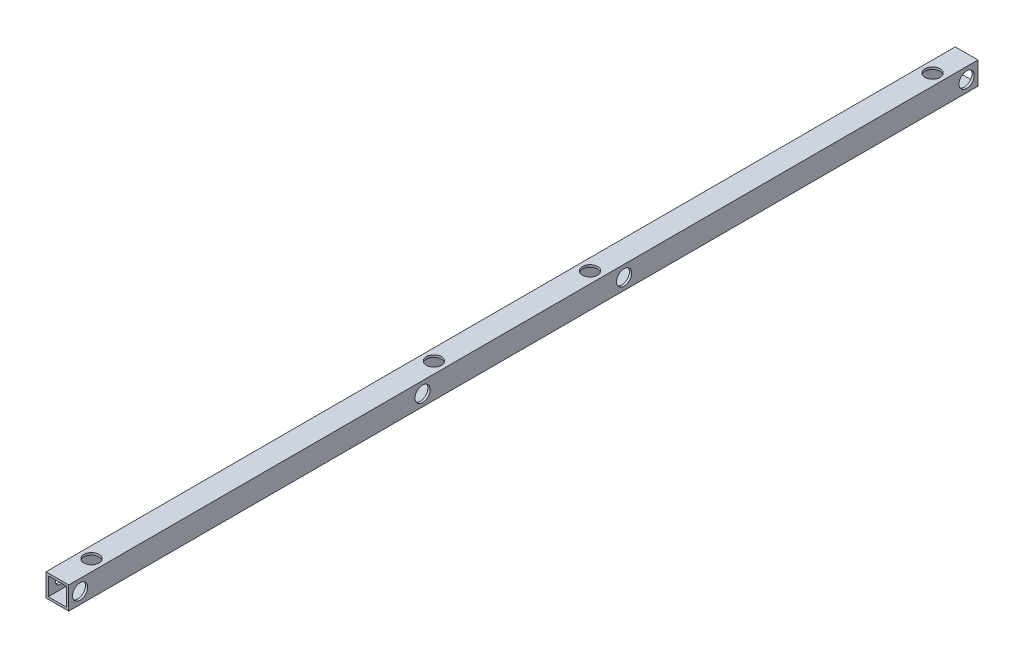
SolidWorks part; units mm, degrees
material "6063-T5"
ref_plane "正面" through (0, 0, 0) normal (0, 0, 1) x (1, 0, 0)
ref_plane "平面" through (0, 0, 0) normal (0, 1, 0) x (1, 0, 0)
ref_plane "右側面" through (0, 0, 0) normal (1, 0, 0) x (0, 0, -1)
sketch "ｽｹｯﾁ1" plane through (0, 0, 0) normal (0, 0, 1) x (1, 0, 0)
  line L1 (-7.5, -7.5) -> (7.5, -7.5)
  line L2 (-7.5, -7.5) -> (-7.5, 7.5)
  line L3 (-7.5, 7.5) -> (7.5, 7.5)
  line L4 (7.5, -7.5) -> (7.5, 7.5)
  line L5 (-7.5, -7.5) -> (7.5, 7.5) construction
  line L6 (-7.5, 7.5) -> (7.5, -7.5) construction
  line L7 (-6, -6) -> (6, -6)
  line L8 (-6, -6) -> (-6, 6)
  line L9 (-6, 6) -> (6, 6)
  line L10 (6, -6) -> (6, 6)
  line L11 (-6, -6) -> (6, 6) construction
  line L12 (-6, 6) -> (6, -6) construction
  point P0 (0, 0)
  point P6 (0, 0)
  dimension "D1" = 1.5
  dimension "D2" = 15
  dimension "D3" = 15
extrude "ﾎﾞｽ - 押し出し1" add sketch "ｽｹｯﾁ1" along normal blind 600
sketch "ｽｹｯﾁ2" plane through (7.5, 0, 0) normal (1, 0, 0) x (0, 0, -1)
  line L0 (-600, -7.5) -> (0, -7.5) construction
  line L1 (0, -7.5) -> (0, 7.5) construction
  line L2 (-600, -7.5) -> (-600, 7.5) construction
  line L3 (-600, 7.5) -> (0, 7.5) construction
  circle A4 centre (-592.5, 0) radius 2.7
  circle A8 centre (-7.5, 0) radius 2.7
  circle A9 centre (-366.5, 0) radius 2.7
  circle A10 centre (-233.5, 0) radius 2.7
  point P12 (-300, 7.5)
  dimension "D1" = 5.4
  dimension "D2" = 7.5
  dimension "D3" = 7.5
  dimension "D6" = 66.5
  dimension "D7" = 2
  dimension "D8" = 133
  dimension "D4" = 7.5
  dimension "D9" = 2
  dimension "D5" = 2
extrude "ｶｯﾄ - 押し出し1" cut sketch "ｽｹｯﾁ2" against normal blind 25
sketch "ｽｹｯﾁ3" plane through (0, 7.5, 0) normal (0, 1, 0) x (1, 0, 0)
  line L2 (7.5, -600) -> (7.5, 0) construction
  line L3 (7.5, 0) -> (-7.5, 0) construction
  circle A1 centre (0, -22.5) radius 2.25
  circle A6 centre (0, -577.5) radius 2.25
  circle A7 centre (0, -351.5) radius 2.25
  circle A8 centre (0, -248.5) radius 2.25
  point P10 (7.5, -300)
  dimension "D2" = 22.5
  dimension "D3" = 4.5
  dimension "D7" = 51.5
  dimension "D8" = 2
  dimension "D9" = 7.5
  dimension "D11" = 22.5
  dimension "D4" = 7.5
  dimension "D5" = 4.5
  dimension "D10" = 51.5
  dimension "D6" = 2
extrude "ｶｯﾄ - 押し出し2" cut sketch "ｽｹｯﾁ3" against normal blind 25
sketch "ｽｹｯﾁ4" plane through (0, 7.5, 0) normal (0, 1, 0) x (1, 0, 0)
  circle A0 centre (0, -577.5) radius 5
  circle A1 centre (0, -351.5) radius 5
  circle A2 centre (0, -248.5) radius 5
  circle A3 centre (0, -22.5) radius 5
  dimension "D1" = 10
  dimension "D2" = 10
  dimension "D3" = 10
  dimension "D4" = 10
extrude "ｶｯﾄ - 押し出し3" cut sketch "ｽｹｯﾁ4" against normal blind 10
sketch "ｽｹｯﾁ5" plane through (7.5, 0, 0) normal (1, 0, 0) x (0, 0, -1)
  circle A0 centre (-592.5, 0) radius 5
  circle A1 centre (-366.5, 0) radius 5
  circle A2 centre (-233.5, 0) radius 5
  circle A3 centre (-7.5, 0) radius 5
  dimension "D1" = 10
  dimension "D2" = 10
  dimension "D3" = 10
  dimension "D4" = 10
extrude "ｶｯﾄ - 押し出し4" cut sketch "ｽｹｯﾁ5" against normal blind 10
